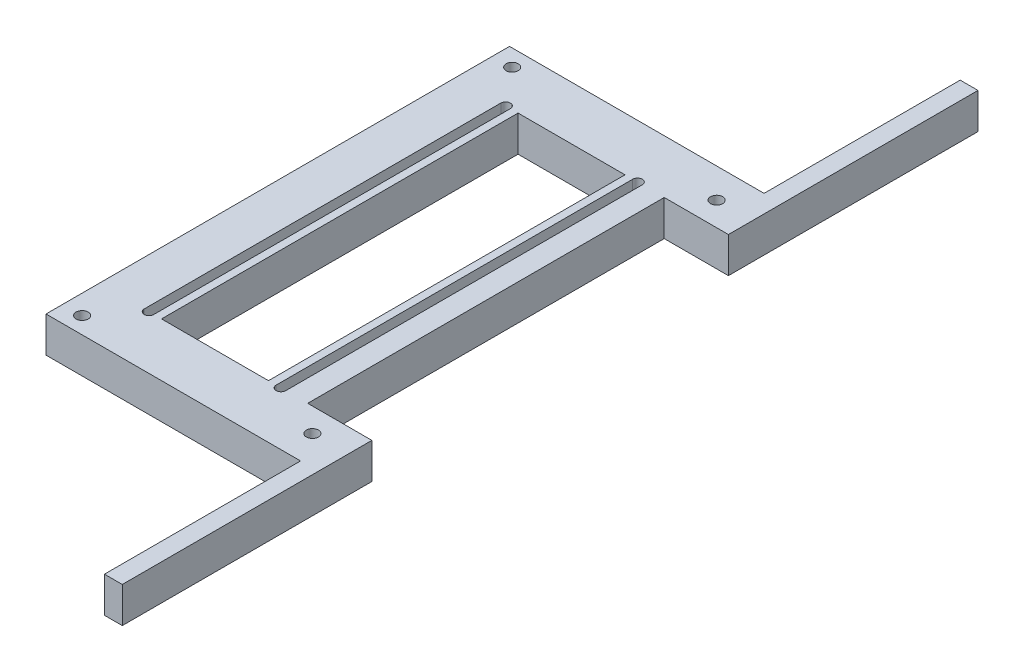
SolidWorks part; units mm, degrees
ref_plane "Front Plane" through (0, 0, 0) normal (0, 0, 1) x (1, 0, 0)
ref_plane "Top Plane" through (0, 0, 0) normal (0, 1, 0) x (1, 0, 0)
ref_plane "Right Plane" through (0, 0, 0) normal (1, 0, 0) x (0, 0, -1)
sketch "Sketch1" plane through (0, 0, 0) normal (0, 1, 0) x (1, 0, 0)
  line L0 (32.2342, -101.7187) -> (32.2342, -31.7187)
  line L1 (32.2342, -31.7187) -> (14.2342, -31.7187)
  line L2 (14.2342, -31.7187) -> (14.2342, 68.2813)
  line L3 (32.2342, -101.7187) -> (27.2342, -101.7187)
  line L4 (27.2342, -101.7187) -> (27.2342, -46.7187)
  line L5 (27.2342, -46.7187) -> (-30.2658, -46.7187)
  line L6 (-30.2658, -46.7187) -> (-44.1621, -46.7187)
  line L7 (22.2342, 24.2187) -> (22.2342, -180.5192) construction
  line L8 (-26.7658, 68.2812) -> (-26.7658, -31.7187)
  line L9 (-26.7658, -31.7187) -> (3.2342, -31.7187)
  line L10 (3.2342, -31.7187) -> (3.2342, 68.2813)
  line L11 (-44.1621, -46.7187) -> (-44.1621, 83.2812)
  line L12 (-44.1621, -46.7187) -> (-26.7658, -31.7187) construction
  line L13 (6.7342, 18.2813) -> (6.7342, -31.7187) construction
  line L14 (8.0842, 18.2813) -> (8.0842, -31.7187)
  line L15 (5.3842, 18.2813) -> (5.3842, -31.7187)
  line L16 (-30.2658, 18.2813) -> (-30.2658, -31.7187) construction
  line L17 (-28.9158, 18.2813) -> (-28.9158, -31.7187)
  line L18 (-31.6158, 18.2813) -> (-31.6158, -31.7187)
  line L19 (-44.1621, 18.2813) -> (14.2342, 18.2813) construction
  line L20 (-44.1621, 83.2812) -> (-26.7658, 68.2812) construction
  line L21 (22.2342, 12.3438) -> (22.2342, 217.0817) construction
  line L22 (-26.7658, 68.2812) -> (3.2342, 68.2813)
  line L23 (-30.2658, 83.2812) -> (-44.1621, 83.2812)
  line L24 (27.2342, 83.2813) -> (-30.2658, 83.2812)
  line L25 (27.2342, 138.2813) -> (27.2342, 83.2813)
  line L26 (32.2342, 138.2813) -> (27.2342, 138.2813)
  line L27 (32.2342, 68.2813) -> (14.2342, 68.2813)
  line L28 (32.2342, 138.2813) -> (32.2342, 68.2813)
  line L29 (-30.2658, 18.2812) -> (-30.2658, 68.2812) construction
  line L30 (-28.9158, 18.2812) -> (-28.9158, 68.2812)
  line L31 (-31.6158, 18.2812) -> (-31.6158, 68.2812)
  line L32 (6.7342, 18.2813) -> (6.7342, 68.2813) construction
  line L33 (8.0842, 18.2813) -> (8.0842, 68.2813)
  line L34 (5.3842, 18.2813) -> (5.3842, 68.2813)
  circle A0 centre (-38.7191, -42.0255) radius 1.7
  arc A1 (8.0842, 18.2813) -> (5.3842, 18.2813) centre (6.7342, 18.2813) ccw
  arc A2 (5.3842, -31.7187) -> (8.0842, -31.7187) centre (6.7342, -31.7187) ccw
  arc A3 (-28.9158, 18.2813) -> (-31.6158, 18.2813) centre (-30.2658, 18.2813) ccw
  arc A4 (-31.6158, -31.7187) -> (-28.9158, -31.7187) centre (-30.2658, -31.7187) ccw
  circle A5 centre (22.2342, -38.4008) radius 1.7
  circle A6 centre (22.2342, 74.9633) radius 1.7
  circle A7 centre (-38.7191, 78.588) radius 1.7
  arc A8 (-28.9158, 18.2812) -> (-31.6158, 18.2812) centre (-30.2658, 18.2813) cw
  arc A9 (-31.6158, 68.2812) -> (-28.9158, 68.2812) centre (-30.2658, 68.2812) cw
  arc A10 (8.0842, 18.2813) -> (5.3842, 18.2813) centre (6.7342, 18.2813) cw
  arc A11 (5.3842, 68.2813) -> (8.0842, 68.2813) centre (6.7342, 68.2813) cw
  point P14 (-26.7658, 18.2813)
  point P19 (6.7342, -6.7187)
  point P24 (-30.2658, -6.7187)
  point P42 (3.2342, 18.2813)
  point P50 (-30.2658, 43.2812)
  point P57 (6.7342, 43.2813)
  dimension "D11" = 2.7
  dimension "D13" = 55
  dimension "D1" = 5
  dimension "D2" = 8
  dimension "D3" = 10
  dimension "D4" = 19
  dimension "D5" = 50
  dimension "D6" = 50
  dimension "D7" = 50
  dimension "D8" = 30
  dimension "D9" = 70
  dimension "D10" = 15
  dimension "D12" = 3.5
  dimension "D14" = 3.5
extrude "Boss-Extrude1" add sketch "Sketch1" along normal blind 10 contours L28 L26 L25 L24 L23 L11 L6 L5 L4 L3 L0 L1 L2 L27 A6 A5 A0 L8 L22 L10 L9 A7 L31 A9 L30 L17 A4 L18 L34 A11 L33 L14 A2 L15
